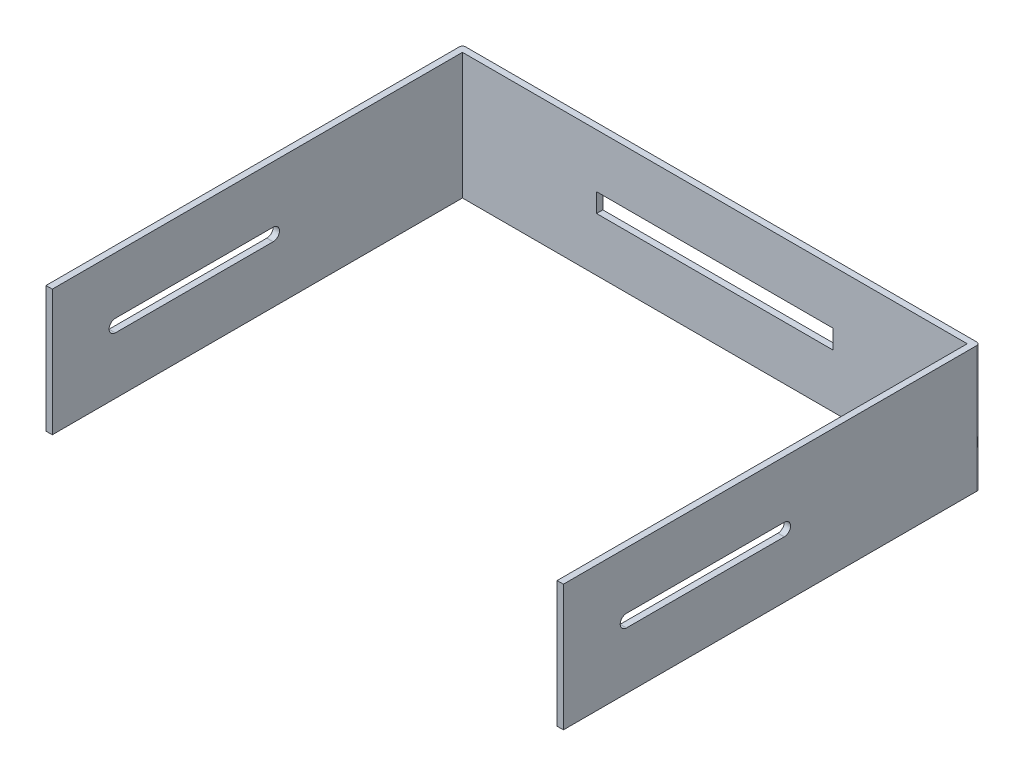
SolidWorks part; units mm, degrees
ref_plane "Plan de face" through (0, 0, 0) normal (0, 0, 1) x (1, 0, 0)
ref_plane "Plan de dessus" through (0, 0, 0) normal (0, 1, 0) x (1, 0, 0)
ref_plane "Plan de droite" through (0, 0, 0) normal (1, 0, 0) x (0, 0, -1)
sketch "Esquisse1" plane through (0, 0, 0) normal (0, 0, 1) x (1, 0, 0)
  line L1 (0, 0) -> (164, 0)
  line L2 (0, 0) -> (0, -40)
  line L3 (0, -40) -> (164, -40)
  line L4 (164, 0) -> (164, -40)
  dimension "D1" = 164
  dimension "D2" = 40
extrude "Boss.-Extru.1" add sketch "Esquisse1" along normal blind 2
sketch "Esquisse2" plane through (0, 0, 2) normal (0, 0, 1) x (1, 0, 0)
  line L0 (0, -40) -> (164, -40) construction
  line L1 (0, 0) -> (2, 0)
  line L2 (0, 0) -> (0, -40)
  line L3 (0, -40) -> (2, -40)
  line L4 (2, 0) -> (2, -40)
  dimension "D1" = 2
extrude "Boss.-Extru.2" add sketch "Esquisse2" along normal blind 130
sketch "Esquisse3" plane through (0, 0, 2) normal (0, 0, 1) x (1, 0, 0)
  line L0 (2, -40) -> (164, -40) construction
  line L1 (164, 0) -> (162, 0)
  line L2 (164, 0) -> (164, -40)
  line L3 (164, -40) -> (162, -40)
  line L4 (162, 0) -> (162, -40)
  dimension "D1" = 2
extrude "Boss.-Extru.3" add sketch "Esquisse3" along normal blind 130
sketch "Esquisse4" plane through (0, 0, 0) normal (-1, 0, 0) x (0, 0, 1)
  line L0 (132, 0) -> (132, -40) construction
  line L1 (132, -40) -> (0, -40) construction
  circle A0 centre (112, -20) radius 2
  dimension "D3" = 4
  dimension "D1" = 20
  dimension "D2" = 20
extrude "Enlèv. mat.-Extru.1" cut sketch "Esquisse4" against normal through all
fillet "Congé1" radius 1 1 edges at (0, -20, 0)
fillet "Congé2" radius 1 1 edges at (164, -20, 0)
sketch "Esquisse5" plane through (0, 0, 2) normal (0, 0, 1) x (1, 0, 0)
  line L4 (162, 0) -> (2, 0) construction
  line L5 (44.5, -17) -> (119.5, -17)
  line L6 (44.5, -17) -> (44.5, -23)
  line L7 (44.5, -23) -> (119.5, -23)
  line L8 (119.5, -17) -> (119.5, -23)
  line L9 (2, -40) -> (2, 0) construction
  dimension "D2" = 6
  dimension "D4" = 42.5
  dimension "D1" = 75
  dimension "D3" = 17
extrude "Enlèv. mat.-Extru.2" cut sketch "Esquisse5" against normal blind 130
sketch "Esquisse6" plane through (0, 0, 0) normal (-1, 0, 0) x (0, 0, 1)
  line L0 (132, 0) -> (1, 0) construction
  line L1 (132, 0) -> (132, -40) construction
  line L2 (62, -18) -> (112, -18)
  line L3 (62, -22) -> (112, -22)
  arc A0 (62, -18) -> (62, -22) centre (62, -20) ccw
  circle A1 centre (112, -20) radius 2 construction
  arc A2 (112, -22) -> (112, -18) centre (112, -20) ccw
  point P4 (132, -20)
  dimension "D1" = 4
  dimension "D4" = 4
  dimension "D2" = 20
  dimension "D3" = 70
extrude "Enlèv. mat.-Extru.3" cut sketch "Esquisse6" against normal through all
